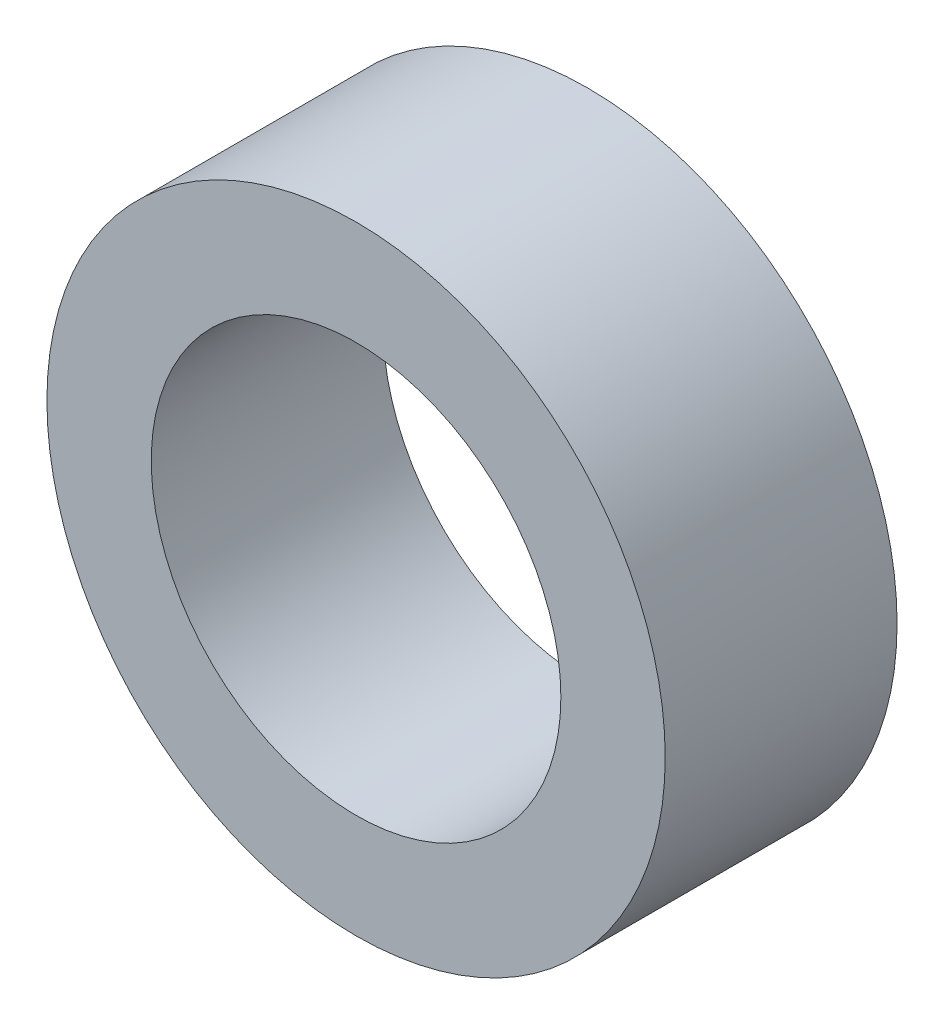
SolidWorks part; units mm, degrees
ref_plane "Front Plane" through (0, 0, 0) normal (0, 0, 1) x (1, 0, 0)
ref_plane "Top Plane" through (0, 0, 0) normal (0, 1, 0) x (1, 0, 0)
ref_plane "Right Plane" through (0, 0, 0) normal (1, 0, 0) x (0, 0, -1)
sketch "Sketch1" plane through (0, 0, 0) normal (0, 0, 1) x (1, 0, 0)
  line L0 (0, 2.65) -> (0, 4) construction
  line L1 (0, -2.65) -> (0, -4) construction
  circle A0 centre (0, 0) radius 4
  circle A1 centre (0, 0) radius 2.65
  dimension "OD" = 8
  dimension "ID" = 5.3
sketch "Sketch2" plane through (0, 0, 0) normal (1, 0, 0) x (0, 0, -1)
  line L0 (-1.5, 2.65) -> (1.5, 2.65) construction
  line L1 (-1.5, -2.65) -> (1.5, -2.65) construction
  line L2 (-1.5, -4) -> (1.5, -4) construction
  line L3 (-1.5, 4) -> (1.5, 4) construction
  dimension "Length" = 3
extrude "Extrude1" add sketch "Sketch1" along normal up to vertex (1.5 mm away) and the other way up to vertex (1.5 mm away) up to point (0, 2.65, 1.5) other way up to point (0, 2.65, -1.5)
sketch "Sketch3" plane through (0, 0, 1.5) normal (0, 0, 1) x (1, 0, 0)
  circle A0 centre (0, 0) radius 2.65 construction
  circle A3 centre (0, 0) radius 2.65
  point P3 (-2.65, 0)
